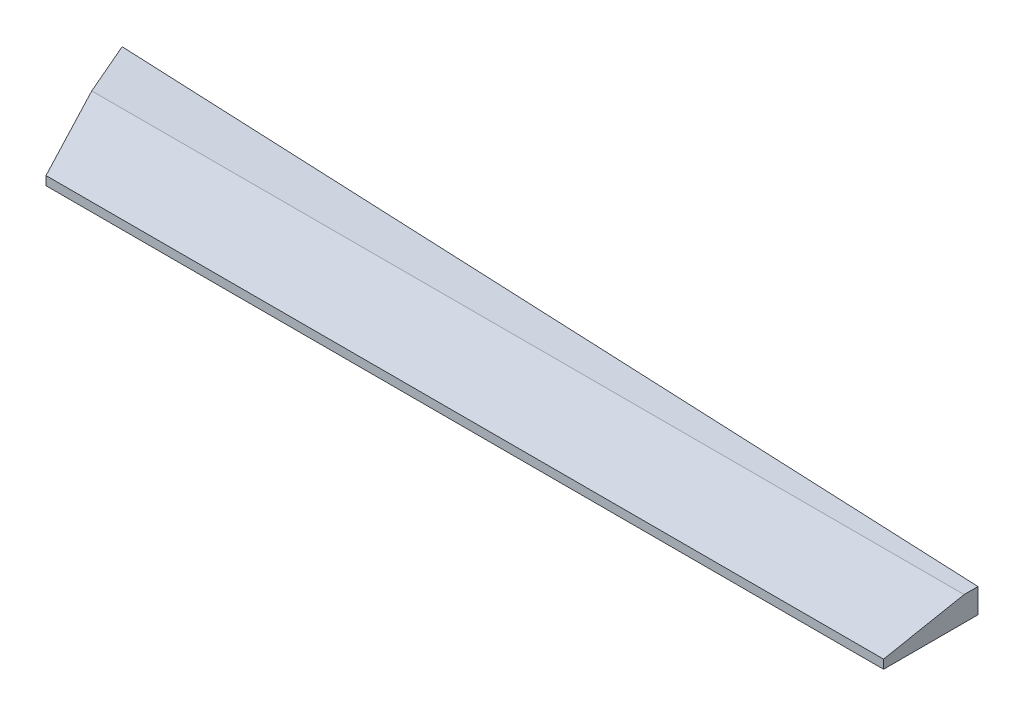
SolidWorks part; units mm, degrees
ref_plane "Front Plane" through (0, 0, 0) normal (0, 0, 1) x (1, 0, 0)
ref_plane "Top Plane" through (0, 0, 0) normal (0, 1, 0) x (1, 0, 0)
ref_plane "Right Plane" through (0, 0, 0) normal (1, 0, 0) x (0, 0, -1)
sketch "Sketch2" plane through (0, 0, 0) normal (0, 1, 0) x (1, 0, 0)
  line L0 (98.0333, -1041.1066) -> (107.0444, -1061.9745)
  line L1 (107.0444, -1061.9745) -> (237.4692, -1061.9745)
  line L2 (98.0333, -1041.1066) -> (237.4692, -1047.2721)
  line L3 (237.4692, -1047.2721) -> (237.4692, -1061.9745)
extrude "Boss-Extrude1" add sketch "Sketch2" along normal blind 3.81
chamfer "Chamfer1" distance 12.54 angle 11 1 edges at (172.2568, 3.81, 1061.9745)
